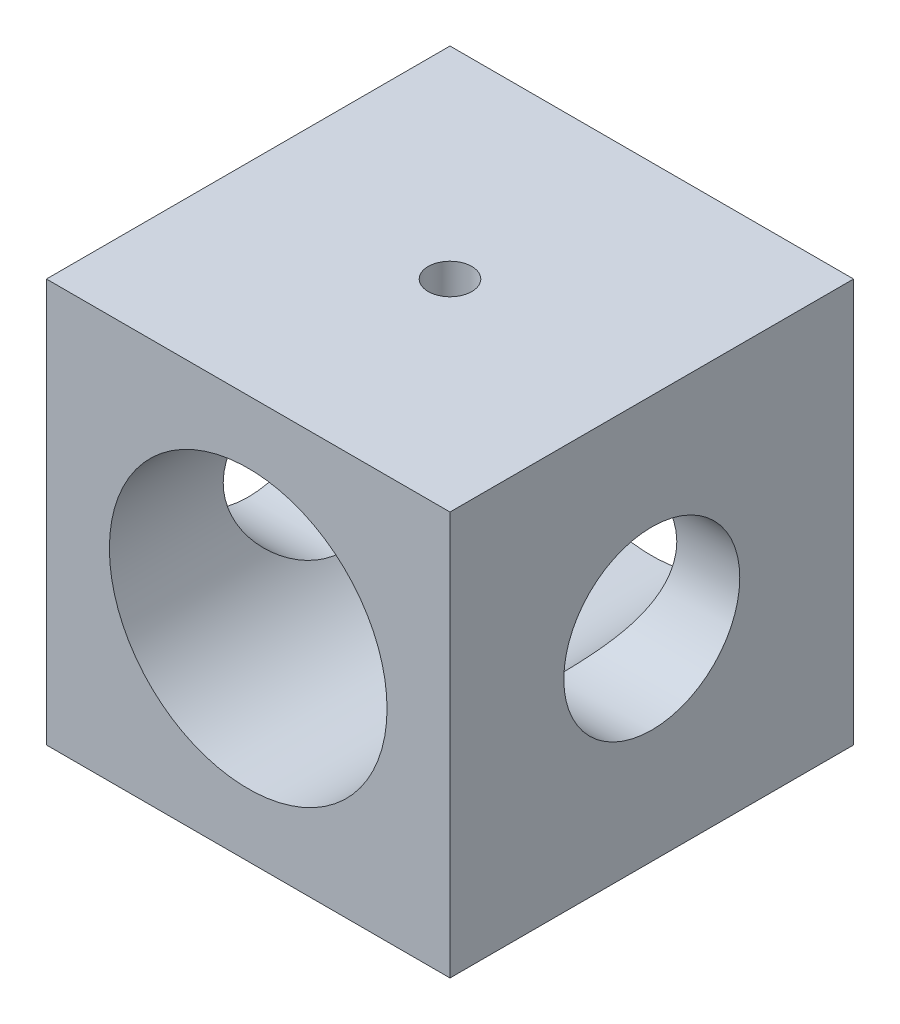
SolidWorks part; units mm, degrees
ref_plane "Front Plane" through (0, 0, 0) normal (0, 0, 1) x (1, 0, 0)
ref_plane "Top Plane" through (0, 0, 0) normal (0, 1, 0) x (1, 0, 0)
ref_plane "Right Plane" through (0, 0, 0) normal (1, 0, 0) x (0, 0, -1)
sketch "Sketch3" plane through (0, 0, 0) normal (0, 1, 0) x (1, 0, 0)
  line L1 (-12.5, -12.5) -> (12.5, -12.5)
  line L2 (-12.5, -12.5) -> (-12.5, 12.5)
  line L3 (-12.5, 12.5) -> (12.5, 12.5)
  line L4 (12.5, -12.5) -> (12.5, 12.5)
  line L5 (-12.5, -12.5) -> (12.5, 12.5) construction
  line L6 (-12.5, 12.5) -> (12.5, -12.5) construction
  point P0 (0, 0)
  dimension "D1" = 25
  dimension "D2" = 25
extrude "Boss-Extrude1" add sketch "Sketch3" along normal blind 25
sketch "Sketch4" plane through (0, 0, 12.5) normal (0, 0, 1) x (1, 0, 0)
  line L0 (12.5, 25) -> (12.5, 0) construction
  circle A0 centre (0, 12.5) radius 8.6
  point P2 (0, 0)
  point P6 (12.5, 12.5)
  dimension "D1" = 17.2
extrude "Cut-Extrude1" cut sketch "Sketch4" against normal up to next
sketch "Sketch5" plane through (0, 25, 0) normal (0, 1, 0) x (1, 0, 0)
  circle A0 centre (0, 0) radius 1.35
  dimension "D1" = 2.7
extrude "Cut-Extrude2" cut sketch "Sketch5" against normal up to next
sketch "Sketch6" plane through (-12.5, 0, 0) normal (-1, 0, 0) x (0, 0, 1)
  line L0 (12.5, 25) -> (12.5, 0) construction
  circle A0 centre (0, 12.5) radius 5.45
  point P2 (0, 0)
  point P6 (12.5, 12.5)
  dimension "D1" = 10.9
extrude "Cut-Extrude3" cut sketch "Sketch6" against normal through all
